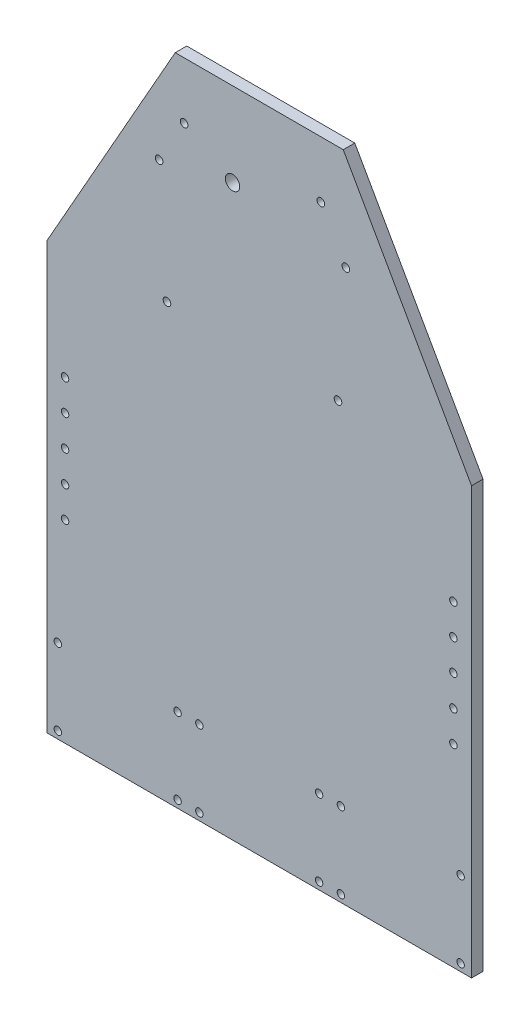
SolidWorks part; units mm, degrees
material "Cedar"
ref_plane "Front Plane" through (0, 0, 0) normal (0, 0, 1) x (1, 0, 0)
ref_plane "Top Plane" through (0, 0, 0) normal (0, 1, 0) x (1, 0, 0)
ref_plane "Right Plane" through (0, 0, 0) normal (1, 0, 0) x (0, 0, -1)
sketch "Sketch1" plane through (0, 0, 0) normal (0, 0, 1) x (1, 0, 0)
  line L0 (120.7244, -111.5408) -> (120.7244, 248.4592)
  line L1 (120.7244, -111.5408) -> (-113.2756, -111.5408)
  line L2 (120.7244, 248.4592) -> (-113.2756, 248.4592)
  line L3 (-113.2756, -111.5408) -> (-113.2756, 248.4592)
  line L4 (120.7244, -111.5408) -> (-113.2756, 248.4592) construction
  line L5 (120.7244, 248.4592) -> (-113.2756, -111.5408) construction
  point P1 (0, 0)
  dimension "D1" = 234
  dimension "D2" = 360
extrude "Boss-Extrude1" add sketch "Sketch1" along normal blind 6.35
sketch "Sketch2" plane through (0, 0, 0) normal (0, 0, -1) x (-1, 0, 0)
  line L0 (-120.7244, -100.8721) -> (-38.9, -100.8721) construction
  line L1 (-120.7244, -111.5408) -> (-120.7244, 248.4592) construction
  line L2 (74.2756, -100.8721) -> (74.2756, -35.021) construction
  line L3 (113.2756, 248.4592) -> (113.2756, -111.5408) construction
  line L7 (-120.7244, 248.4592) -> (113.2756, 248.4592) construction
  line L10 (-50.0244, 248.4592) -> (-120.7244, 123.3955)
  line L11 (-120.7244, 123.3955) -> (-120.7244, 248.4592)
  line L12 (-120.7244, 248.4592) -> (-50.0244, 248.4592)
  line L13 (42.5756, 248.4592) -> (99.1068, 148.4592) construction
  line L14 (-106.5556, 148.4592) -> (-50.0244, 248.4592) construction
  line L15 (113.2756, 248.4592) -> (42.5756, 248.4592)
  line L16 (113.2756, 123.3955) -> (113.2756, 248.4592)
  line L17 (42.5756, 248.4592) -> (113.2756, 123.3955)
  circle A0 centre (107.2756, -107.5408) radius 2.05
  circle A1 centre (107.2756, -65.5408) radius 2.05
  circle A2 centre (107.2756, -65.5408) radius 1.85 construction
  circle A3 centre (41.2756, -107.5408) radius 2.05
  circle A4 centre (41.2756, -65.5408) radius 2.05
  circle A5 centre (29.2756, -107.5408) radius 2.05
  circle A6 centre (29.2756, -65.5408) radius 2.05
  circle A7 centre (-36.7244, -107.5408) radius 2.05
  circle A8 centre (-36.7244, -65.5408) radius 2.05
  circle A9 centre (-48.7244, -107.5408) radius 2.05
  circle A10 centre (-48.7244, -65.5408) radius 2.05
  circle A11 centre (-114.7244, -107.5408) radius 2.05
  circle A12 centre (-114.7244, -65.5408) radius 2.05
  circle A13 centre (10.987, 202.2553) radius 3.9687
  circle A14 centre (-110.7244, -4.8799) radius 2.05
  circle A15 centre (103.2756, -4.8799) radius 2.05
  circle A16 centre (103.2756, 12.1201) radius 2.05
  circle A17 centre (-110.7244, 12.1201) radius 2.05
  circle A18 centre (103.2756, 29.1201) radius 2.05
  circle A19 centre (-110.7244, 29.1201) radius 2.05
  circle A20 centre (103.2756, 46.1201) radius 2.05
  circle A21 centre (-110.7244, 46.1201) radius 2.05
  circle A22 centre (103.2756, 63.1201) radius 2.05
  circle A23 centre (-110.7244, 63.1201) radius 2.05
  circle A28 centre (37.6829, 217.2553) radius 2.1
  circle A29 centre (41.2756, -107.5408) radius 1.85 construction
  circle A30 centre (51.4623, 192.8806) radius 2.1
  circle A31 centre (47.1312, 127.2553) radius 2.1
  circle A32 centre (-37.6829, 217.2553) radius 2.1
  circle A33 centre (-47.1312, 127.2553) radius 2.1
  circle A34 centre (-51.4623, 192.8806) radius 2.1
  circle A36 centre (103.2756, -4.8799) radius 1.85 construction
  circle A37 centre (-110.7244, -4.8799) radius 1.85 construction
  point P7 (0, 0)
  point P39 (10.987, 202.2553)
  point P61 (0, 0)
  point P64 (119.5438, 172.1927)
  point P66 (113.2756, 133.4592)
  point P78 (0, 0)
  point P79 (0, 0)
  point P85 (0, 0)
  point P86 (0, 0)
  point P87 (0, 0)
  point P88 (0, 0)
  point P89 (0, 0)
  point P90 (0, 0)
  point P93 (0, 0)
  point P94 (0, 0)
  point P101 (0, 0)
  point P104 (0, 0)
  point P105 (0, 0)
  point P107 (0, 0)
  point P112 (0, 0)
  point P115 (0, 0)
  point P116 (0, 0)
  dimension "D1" = 4.1
  dimension "D4" = 4.1
  dimension "3/8in" = 7.9375
  dimension "D6" = 4.2
  dimension "117" = 17
  dimension "D8" = 46.2038
  dimension "D3" = 3
  dimension "D5" = 5
extrude "Cut-Extrude1" cut sketch "Sketch2" against normal blind 10
sketch "Sketch3" [suppressed] plane through (0, 0, 6.35) normal (0, 0, 1) x (1, 0, 0)
  line L0 (44.7849, 222.2553) -> (-44.7849, 222.2553) construction
  line L1 (-111.3, 222.2553) -> (111.3, 222.2553)
  line L2 (-111.3, 222.2553) -> (-111.3, -111.5408)
  line L3 (-111.3, -111.5408) -> (111.3, -111.5408)
  line L4 (111.3, 222.2553) -> (111.3, -111.5408)
sketch "Sketch4" [suppressed] plane through (0, 0, 6.35) normal (0, 0, 1) x (1, 0, 0)
  line L0 (21.5, -92.0408) -> (21.5, -51.0408) construction
  line L1 (-95.7, -51.0408) -> (-52.7, -51.0408)
  line L2 (-95.7, -51.0408) -> (-95.7, -92.0408)
  line L3 (-95.7, -92.0408) -> (-52.7, -92.0408)
  line L4 (-52.7, -51.0408) -> (-52.7, -92.0408)
  line L13 (-21.5, -51.0408) -> (21.5, -51.0408)
  line L14 (-21.5, -51.0408) -> (-21.5, -92.0408)
  line L15 (-21.5, -92.0408) -> (21.5, -92.0408)
  line L16 (21.5, -51.0408) -> (21.5, -92.0408)
  line L18 (52.7, -51.0408) -> (95.7, -51.0408)
  line L19 (52.7, -51.0408) -> (52.7, -92.0408)
  line L20 (52.7, -92.0408) -> (95.7, -92.0408)
  line L21 (95.7, -51.0408) -> (95.7, -92.0408)
extrude "Boss-Extrude2" [suppressed] add sketch "Sketch4" against normal up to surface (6.35 mm away)
sketch "Sketch6" [suppressed] plane through (0, 0, 0) normal (0, 0, -1) x (-1, 0, 0)
  line L0 (0, -111.5408) -> (0, 222.2553) construction
  line L1 (111.3, -111.5408) -> (-111.3, -111.5408) construction
  line L2 (-44.7849, 222.2553) -> (44.7849, 222.2553) construction
  line L3 (0, 152.2553) -> (-25, 152.2553)
  line L4 (-33.3205, 147.8023) -> (-53.3205, 117.8023)
  line L5 (-55, 112.2553) -> (-55, -11.5408)
  line L6 (-45, -21.5408) -> (45, -21.5408)
  line L7 (55, 112.2553) -> (55, -11.5408)
  line L8 (33.3205, 147.8023) -> (53.3205, 117.8023)
  line L9 (0, 152.2553) -> (25, 152.2553)
  arc A0 (-55, -11.5408) -> (-45, -21.5408) centre (-45, -11.5408) ccw
  arc A1 (-53.3205, 117.8023) -> (-55, 112.2553) centre (-45, 112.2553) ccw
  arc A2 (-25, 152.2553) -> (-33.3205, 147.8023) centre (-25, 142.2553) ccw
  arc A3 (25, 152.2553) -> (33.3205, 147.8023) centre (25, 142.2553) cw
  arc A4 (53.3205, 117.8023) -> (55, 112.2553) centre (45, 112.2553) cw
  arc A5 (55, -11.5408) -> (45, -21.5408) centre (45, -11.5408) cw
  point P17 (-12.5, 152.2553)
  point P28 (0, -21.5408)
  dimension "D1" = 10
  dimension "D2" = 55
  dimension "D3" = 90
  dimension "D4" = 40
  dimension "D5" = 25
  dimension "D6" = 70
extrude "Cut-Extrude3" [suppressed] cut sketch "Sketch6" against normal up to surface (6.35 mm away)
